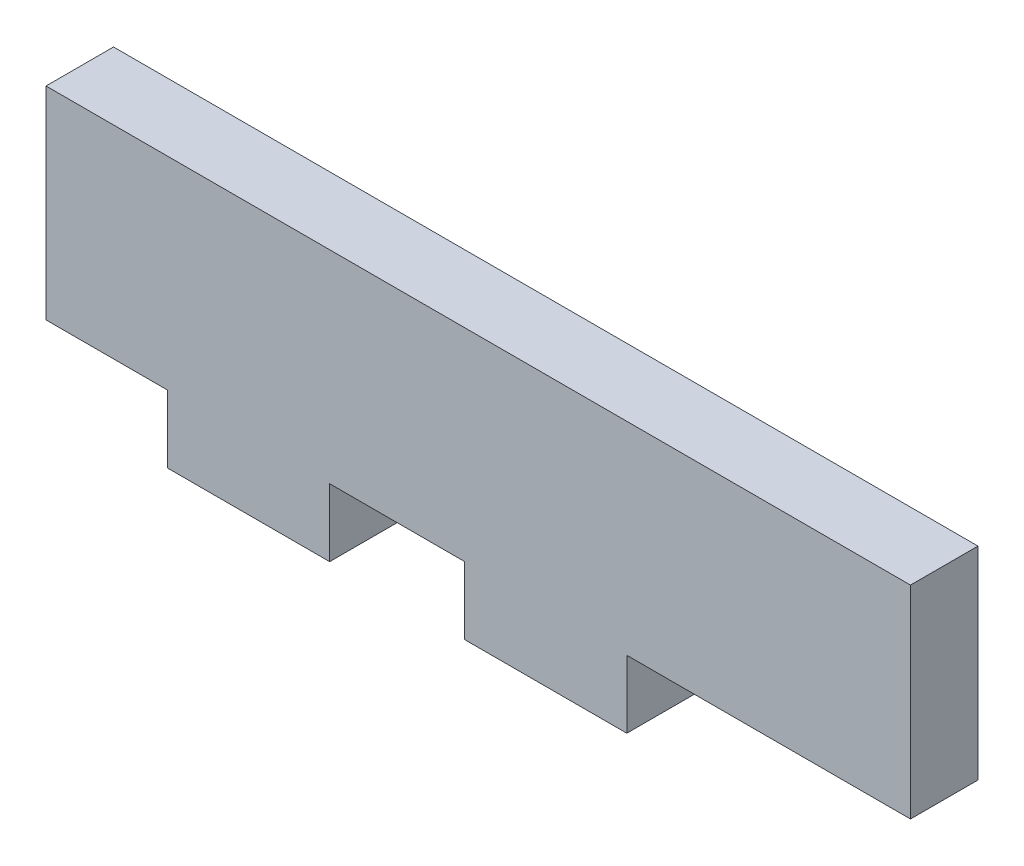
SolidWorks part; units mm, degrees
ref_plane "Front Plane" through (0, 0, 0) normal (0, 0, 1) x (1, 0, 0)
ref_plane "Top Plane" through (0, 0, 0) normal (0, 1, 0) x (1, 0, 0)
ref_plane "Right Plane" through (0, 0, 0) normal (1, 0, 0) x (0, 0, -1)
sketch "Sketch1" plane through (0, 0, 0) normal (0, 0, 1) x (1, 0, 0)
  line L1 (0, 0) -> (81.28, 0)
  line L2 (0, 0) -> (0, 19.05)
  line L3 (0, 19.05) -> (81.28, 19.05)
  line L4 (81.28, 0) -> (81.28, 19.05)
  line L9 (11.43, 0) -> (26.67, 0)
  line L10 (11.43, 0) -> (11.43, -6.35)
  line L11 (11.43, -6.35) -> (26.67, -6.35)
  line L12 (26.67, 0) -> (26.67, -6.35)
  line L13 (39.37, 0) -> (54.61, 0)
  line L14 (39.37, 0) -> (39.37, -6.35)
  line L15 (39.37, -6.35) -> (54.61, -6.35)
  line L16 (54.61, 0) -> (54.61, -6.35)
  dimension "D1" = 81.28
  dimension "D2" = 19.05
  dimension "D3" = 11.43
  dimension "D4" = 15.24
  dimension "D5" = 6.35
  dimension "D6" = 15.24
  dimension "D7" = 6.35
  dimension "D8" = 12.7
extrude "Boss-Extrude1" add sketch "Sketch1" along normal blind 6.35 contours L12 L1 L10 L11 | L1 L4 L3 L2 | L16 L1 L14 L15
